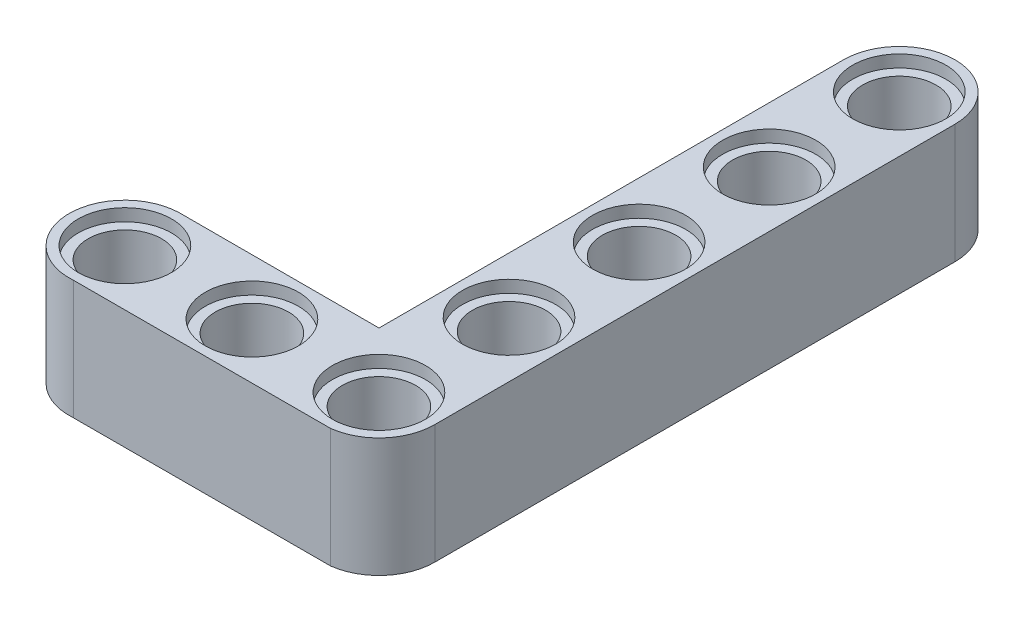
SolidWorks part; units mm, degrees
ref_plane "Front Plane" through (0, 0, 0) normal (0, 0, 1) x (1, 0, 0)
ref_plane "Top Plane" through (0, 0, 0) normal (0, 1, 0) x (1, 0, 0)
ref_plane "Right Plane" through (0, 0, 0) normal (1, 0, 0) x (0, 0, -1)
sketch "Sketch1" plane through (0, 0, 0) normal (0, 1, 0) x (1, 0, 0)
  line L0 (-39.1656, -18.6318) -> (-22.5356, -18.6318) construction
  line L1 (-39.2561, -14.9819) -> (-26.1826, -14.9806)
  line L2 (-38.8975, -22.273) -> (-22.0733, -22.256)
  line L3 (-22.5356, -18.6318) -> (-22.5356, 15.4282) construction
  line L4 (-26.1826, -14.9806) -> (-26.1856, 15.4282)
  line L5 (-18.8822, -18.6024) -> (-18.8856, 15.4282)
  line L6 (-22.5356, -10.1168) -> (-14.1229, -10.1168) construction
  line L7 (-22.5356, -1.6018) -> (-14.1229, -1.6018) construction
  line L8 (-22.5356, 6.9132) -> (-12.6229, 6.9132) construction
  arc A0 (-39.2561, -14.9819) -> (-38.8975, -22.273) centre (-39.1656, -18.6318) ccw
  arc A1 (-22.0733, -22.256) -> (-18.8822, -18.6024) centre (-22.5356, -18.6318) ccw
  circle A2 centre (-39.1656, -18.6318) radius 2.4
  circle A3 centre (-30.8506, -18.6318) radius 2.4
  circle A4 centre (-22.5356, -18.6318) radius 2.4
  arc A6 (-18.8856, 15.4282) -> (-26.1856, 15.4282) centre (-22.5356, 15.4282) ccw
  circle A7 centre (-22.5356, 15.4282) radius 2.4
  circle A8 centre (-22.5356, 6.9132) radius 2.4
  circle A9 centre (-22.5356, -1.6018) radius 2.4
  circle A10 centre (-22.5356, -10.1168) radius 2.4
  point P2 (-30.6754, -18.5405)
  point P13 (-22.9424, -6.6711)
  dimension "D3" = 8.515
  dimension "D4" = 8.515
  dimension "D9" = 3.6483
  dimension "D10" = 3.65
  dimension "D12" = 3.6525
  dimension "D1" = 7.3
  dimension "D2" = 8.515
  dimension "D5" = 8.515
  dimension "D6" = 8.315
  dimension "D7" = 8.315
  dimension "D8" = 7.3
  dimension "D11" = 3.6508
  dimension "D13" = 9.9127
extrude "Boss-Extrude1" add sketch "Sketch1" along normal blind 7.8
sketch "Sketch2" plane through (0, 7.8, 0) normal (0, 1, 0) x (1, 0, 0)
  circle A0 centre (-39.1656, -18.6318) radius 3.05
  circle A1 centre (-30.8506, -18.6318) radius 3.05
  circle A2 centre (-22.5356, -18.6318) radius 3.05
  circle A3 centre (-22.5356, -10.1168) radius 3.05
  circle A4 centre (-22.5356, -1.6018) radius 3.05
  circle A5 centre (-22.5356, 6.9132) radius 3.05
  circle A6 centre (-22.5356, 15.4282) radius 3.05
extrude "Cut-Extrude1" cut sketch "Sketch2" against normal blind 0.8
sketch "Sketch3" plane through (0, 0, 0) normal (0, -1, 0) x (1, 0, 0)
  circle A0 centre (-30.8506, 18.6318) radius 3.05
  circle A1 centre (-39.1656, 18.6318) radius 3.05
  circle A2 centre (-22.5356, 18.6318) radius 3.05
  circle A3 centre (-22.5356, 10.1168) radius 3.05
  circle A4 centre (-22.5356, 1.6018) radius 3.05
  circle A5 centre (-22.5356, -6.9132) radius 3.05
  circle A6 centre (-22.5356, -15.4282) radius 3.05
extrude "Cut-Extrude2" cut sketch "Sketch3" against normal blind 0.8
sketch "Sketch5" plane through (0, 7.8, 0) normal (0, 1, 0) x (1, 0, 0)
sketch "Sketch6" plane through (0, 7.8, 0) normal (0, 1, 0) x (1, 0, 0)
  line L0 (-39.1656, -18.6318) -> (-22.5356, -18.6318)
  line L1 (-22.5356, -18.6318) -> (-22.5356, 6.9132)
  dimension "D1" = 16.63
  dimension "D2" = 25.545
